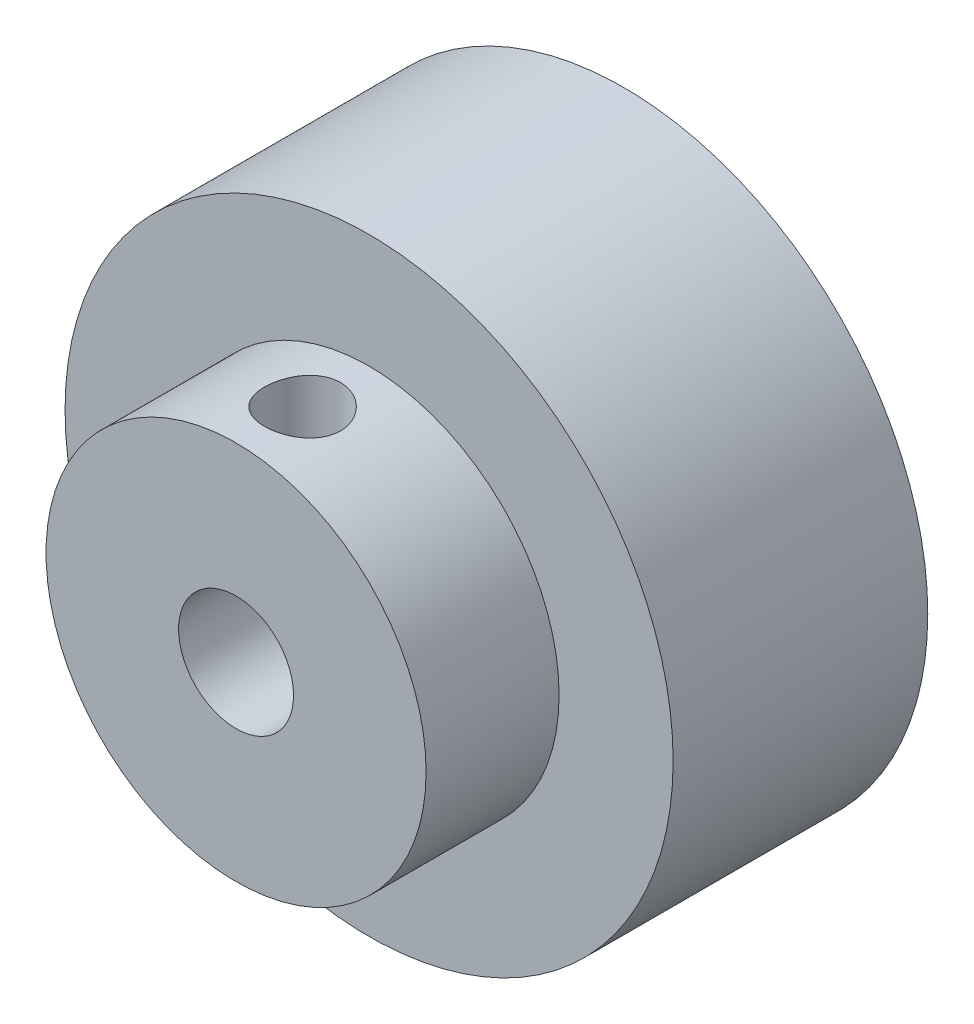
SolidWorks part; units mm, degrees
ref_plane "Plan de face" through (0, 0, 0) normal (0, 0, 1) x (1, 0, 0)
ref_plane "Plan de dessus" through (0, 0, 0) normal (0, 1, 0) x (1, 0, 0)
ref_plane "Plan de droite" through (0, 0, 0) normal (1, 0, 0) x (0, 0, -1)
sketch "Esquisse1" plane through (0, 0, 0) normal (0, 0, 1) x (1, 0, 0)
  circle A0 centre (0, 0) radius 3.1
  circle A1 centre (0, 0) radius 16
  dimension "D1" = 6.2
  dimension "D2" = 32
extrude "Boss.-Extru.1" add sketch "Esquisse1" along normal mid plane 13.4
sketch "Esquisse2" plane through (0, 0, 0) normal (0, 0, 1) x (1, 0, 0)
  circle A0 centre (0, 0) radius 7.85
  circle A1 centre (0, 0) radius 13.6604
  dimension "D1" = 15.7
extrude "Enlèv. mat.-Extru.1" cut sketch "Esquisse2" against normal mid plane 10.3
sketch "Esquisse4" plane through (0, 0, 6.7) normal (0, 0, 1) x (1, 0, 0)
  circle A0 centre (0, 0) radius 10
  circle A1 centre (0, 0) radius 3.025
  dimension "D1" = 20
extrude "Boss.-Extru.2" add sketch "Esquisse4" along normal blind 7
sketch "Esquisse5" plane through (0, 0, 0) normal (0, 1, 0) x (1, 0, 0)
  line L0 (-10, -13.7) -> (10, -13.7) construction
  circle A0 centre (0, -10.2) radius 2
  dimension "D1" = 4
  dimension "D2" = 3.5
extrude "Enlèv. mat.-Extru.3" cut sketch "Esquisse5" along normal through all
ref_plane "Plane1" through (0, 0, 0) normal (0, 0, 1) x (1, 0, 0)
